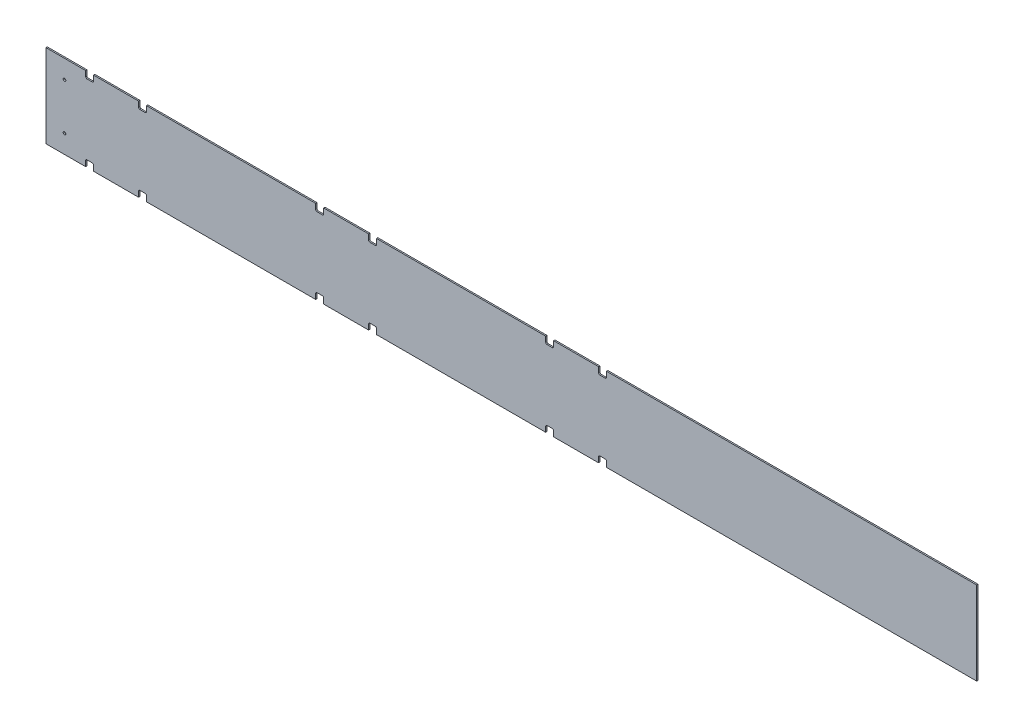
SolidWorks part; units mm, degrees
material "PC High Viscosity"
ref_plane "Front Plane" through (0, 0, 0) normal (0, 0, 1) x (1, 0, 0)
ref_plane "Top Plane" through (0, 0, 0) normal (0, 1, 0) x (1, 0, 0)
ref_plane "Right Plane" through (0, 0, 0) normal (1, 0, 0) x (0, 0, -1)
sketch "Sketch1" plane through (0, 0, 0) normal (0, 0, 1) x (1, 0, 0)
  line L1 (-1117.6, -100.0125) -> (1117.6, -100.0125)
  line L2 (-1117.6, -100.0125) -> (-1117.6, 100.0125)
  line L3 (-1117.6, 100.0125) -> (1117.6, 100.0125)
  line L4 (1117.6, -100.0125) -> (1117.6, 100.0125)
  line L5 (-1117.6, -100.0125) -> (1117.6, 100.0125) construction
  line L6 (-1117.6, 100.0125) -> (1117.6, -100.0125) construction
  point P0 (0, 0)
  dimension "D1" = 200.025
  dimension "D2" = 2235.2
extrude "Boss-Extrude1" add sketch "Sketch1" along normal blind 3.175
sketch "Sketch2" plane through (0, 0, 0) normal (0, 0, -1) x (-1, 0, 0)
  line L0 (1117.6, -100.0125) -> (-1117.6, -100.0125) construction
  line L1 (-228.6, -100.0125) -> (-209.55, -100.0125)
  line L2 (-228.6, -100.0125) -> (-228.6, -84.1375)
  line L3 (-228.6, -84.1375) -> (-209.55, -84.1375)
  line L4 (-209.55, -100.0125) -> (-209.55, -84.1375)
  line L5 (-1117.6, -100.0125) -> (-1117.6, 100.0125) construction
  line L6 (-101.6, -100.0125) -> (-101.6, -84.1375)
  line L7 (-101.6, -100.0125) -> (-82.55, -100.0125)
  line L8 (-82.55, -100.0125) -> (-82.55, -84.1375)
  line L9 (-101.6, -84.1375) -> (-82.55, -84.1375)
  line L10 (-228.6, -100.0125) -> (-101.6, -100.0125) construction
  line L11 (323.85, -100.0125) -> (323.85, -84.1375)
  line L12 (323.85, -100.0125) -> (342.9, -100.0125)
  line L13 (342.9, -100.0125) -> (342.9, -84.1375)
  line L14 (323.85, -84.1375) -> (342.9, -84.1375)
  line L15 (450.85, -100.0125) -> (450.85, -84.1375)
  line L16 (450.85, -84.1375) -> (469.9, -84.1375)
  line L17 (469.9, -100.0125) -> (469.9, -84.1375)
  line L18 (450.85, -100.0125) -> (469.9, -100.0125)
  line L19 (876.3, -100.0125) -> (876.3, -84.1375)
  line L20 (876.3, -100.0125) -> (895.35, -100.0125)
  line L21 (895.35, -100.0125) -> (895.35, -84.1375)
  line L22 (876.3, -84.1375) -> (895.35, -84.1375)
  line L23 (1003.3, -100.0125) -> (1003.3, -84.1375)
  line L24 (1003.3, -84.1375) -> (1022.35, -84.1375)
  line L25 (1022.35, -100.0125) -> (1022.35, -84.1375)
  line L26 (1003.3, -100.0125) -> (1022.35, -100.0125)
  line L27 (-228.6, -100.0125) -> (323.85, -100.0125) construction
  point P6 (-219.075, -100.0125)
  dimension "D1" = 15.875
  dimension "D2" = 19.05
  dimension "D3" = 898.525
  dimension "D4" = 2
  dimension "D5" = 127
  dimension "D6" = 3
  dimension "D7" = 552.45
extrude "Cut-Extrude1" cut sketch "Sketch2" against normal through all
sketch "Sketch3" plane through (0, 0, 0) normal (0, 0, -1) x (-1, 0, 0)
  line L0 (1073.15, 100.0125) -> (1073.15, -100.0125) construction
  line L1 (-1117.6, 100.0125) -> (1117.6, 100.0125) construction
  line L2 (1117.6, -100.0125) -> (1022.35, -100.0125) construction
  line L3 (1117.6, 100.0125) -> (1117.6, -100.0125) construction
  point P8 (1073.15, -55.5625)
  point P9 (1073.15, 55.5625)
  dimension "D1" = 44.45
  dimension "D2" = 44.45
  dimension "D3" = 44.45
hole_wizard "1/4 (0.25) Diameter Hole1" positions "Sketch4" profile "Sketch5" hole size "1/4" standard "ANSI Inch" end condition through all
sketch "Sketch4" plane through (0, 0, 0) normal (0, 0, -1) x (-1, 0, 0)
  point P0 (1073.15, -55.5625)
  point P3 (1073.15, 55.5625)
sketch "Sketch5" plane through (-1073.15, -55.5625, 0) normal (1, 0, 0) x (0, 1, 0)
  line L0 (0, 0) -> (0, 3.175)
  line L1 (0, 3.175) -> (3.175, 3.175)
  line L2 (3.175, 3.175) -> (3.175, 0)
  line L5 (3.175, 0) -> (0, 0)
  line L11 (0, -6.35) -> (0, 107.95) construction
  dimension "Thru Hole Dia." = 6.35
  dimension "Thru Hole Depth" = 3.175
fillet "Fillet1" radius 3.175 12 edges at (-1022.35, -84.1375, 1.5875) (-1003.3, -84.1375, 1.5875) (-876.3, -84.1375, 1.5875) (-895.35, -84.1375, 1.5875) (-469.9, -84.1375, 1.5875) (-450.85, -84.1375, 1.5875) (-342.9, -84.1375, 1.5875) (-323.85, -84.1375, 1.5875) (101.6, -84.1375, 1.5875) (82.55, -84.1375, 1.5875) (209.55, -84.1375, 1.5875) (228.6, -84.1375, 1.5875)
mirror "Mirror1" about plane through (0, 0, 0) normal (0, 1, 0) of "Fillet1", "Cut-Extrude1"
